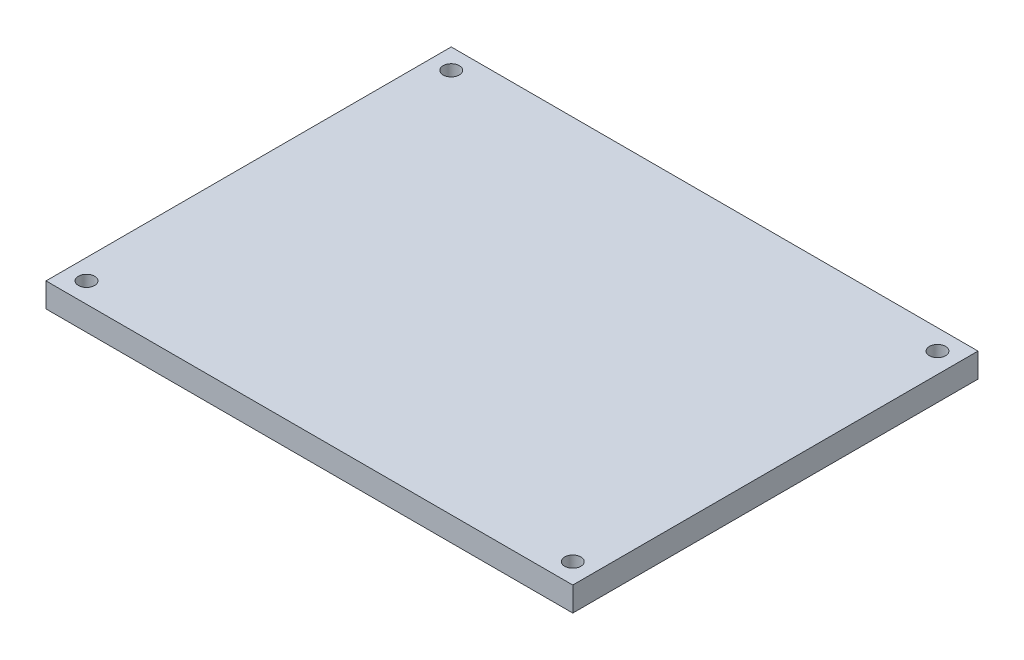
SolidWorks part; units mm, degrees
material "Balsa"
ref_plane "Front Plane" through (0, 0, 0) normal (0, 0, 1) x (1, 0, 0)
ref_plane "Top Plane" through (0, 0, 0) normal (0, 1, 0) x (1, 0, 0)
ref_plane "Right Plane" through (0, 0, 0) normal (1, 0, 0) x (0, 0, -1)
sketch "Sketch1" plane through (0, 0, 0) normal (0, 1, 0) x (1, 0, 0)
  line L1 (-65, 50) -> (65, 50)
  line L2 (-65, 50) -> (-65, -50)
  line L3 (-65, -50) -> (65, -50)
  line L4 (65, 50) -> (65, -50)
  line L5 (-65, 50) -> (65, -50) construction
  line L6 (-65, -50) -> (65, 50) construction
  point P0 (0, 0)
  dimension "D1" = 130
  dimension "D2" = 100
extrude "Boss-Extrude1" add sketch "Sketch1" along normal blind 6
sketch "Sketch3" plane through (0, 6, 0) normal (0, 1, 0) x (1, 0, 0)
  line L0 (65, 50) -> (-65, 50) construction
  line L1 (-65, 50) -> (-65, -50) construction
  line L2 (0, 63.2223) -> (0, -58.6127) construction
  line L3 (-91.1583, 0) -> (85.2249, 0) construction
  circle A0 centre (-60, 45) radius 2
  circle A1 centre (-60, -45) radius 2
  circle A2 centre (60, -45) radius 2
  circle A3 centre (60, 45) radius 2
  point P0 (-60, 45)
  dimension "D3" = 4
  dimension "D1" = 5
  dimension "D2" = 5
extrude "Cut-Extrude1" cut sketch "Sketch3" against normal through all
